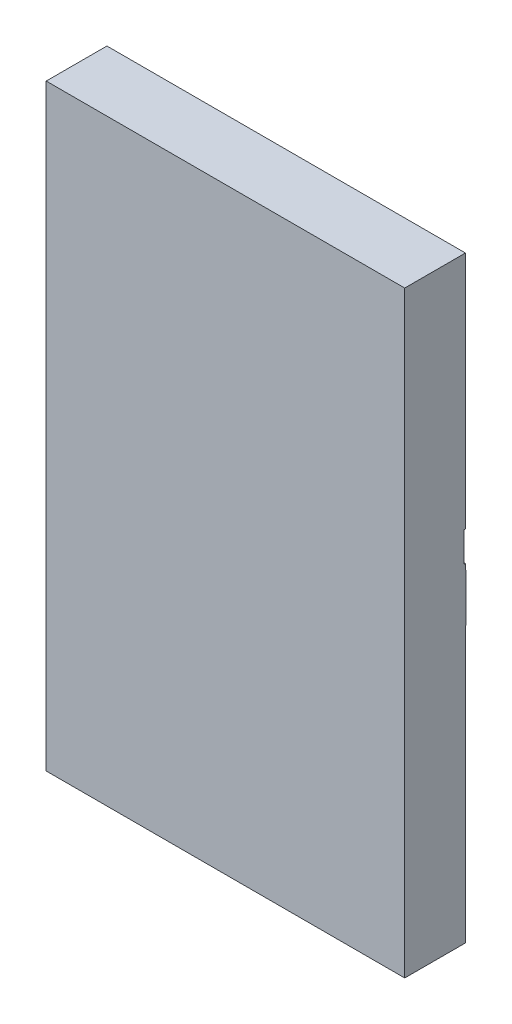
SolidWorks part; units mm, degrees
ref_plane "Front" through (0, 0, 0) normal (0, 0, 1) x (1, 0, 0)
ref_plane "Top" through (0, 0, 0) normal (0, 1, 0) x (1, 0, 0)
ref_plane "Right" through (0, 0, 0) normal (1, 0, 0) x (0, 0, -1)
sketch "Sketch1" plane through (0, 0, 0) normal (0, 0, 1) x (1, 0, 0)
  line L1 (0, 0) -> (3, 0)
  line L2 (0, 0) -> (0, 5)
  line L3 (0, 5) -> (3, 5)
  line L4 (3, 0) -> (3, 5)
  dimension "D1" = 5
  dimension "D2" = 3
extrude "Base-Extrude" add sketch "Sketch1" along normal blind 0.508
sketch "Sketch2" plane through (3, 0, 0) normal (1, 0, 0) x (0, 0, -1)
  line L0 (0, 0) -> (0, 5) construction
  line L1 (0, 3) -> (-0.01, 3)
  line L2 (0, 3) -> (0, 2.75)
  line L3 (0, 2.75) -> (-0.01, 2.75)
  line L4 (-0.01, 3) -> (-0.01, 2.75)
  line L5 (-0.508, 5) -> (0, 5) construction
  dimension "D1" = 2
  dimension "D2" = 0.25
  dimension "D3" = 0.01
extrude "Cut-Extrude1" cut sketch "Sketch2" against normal through all
sketch "Sketch3" plane through (3, 0, 0) normal (1, 0, 0) x (0, 0, -1)
  line L0 (0, 0) -> (0, 2.75) construction
  line L1 (0, 2.7) -> (0.003, 2.7)
  line L2 (0, 2.7) -> (0, 2.3)
  line L3 (0, 2.3) -> (0.003, 2.3)
  line L4 (0.003, 2.7) -> (0.003, 2.3)
  line L5 (-0.508, 0) -> (0, 0) construction
  dimension "D1" = 0.4
  dimension "D2" = 2.3
  dimension "D3" = 0.003
extrude "Boss-Extrude2" add sketch "Sketch3" against normal blind 3
sketch "Sketch4" plane through (0, 0, 0) normal (0, 0, -1) x (-1, 0, 0)
  line L5 (-3, 0) -> (-3, 2.3) construction
  line L7 (0, 2.3) -> (-3, 2.3) construction
  circle A0 centre (-2.9, 2.2) radius 0.02
  dimension "D1" = 0.04
  dimension "Vertical Edge Distance" = 0.1
split line "Split Line10"
sketch "Sketch9" plane through (0, 0, 0) normal (0, 0, -1) x (-1, 0, 0)
  line L0 (-3, 5) -> (0, 5) construction
  line L1 (-2.95, 4.95) -> (-0.05, 4.95)
  line L2 (-2.95, 4.95) -> (-2.95, 3)
  line L3 (0, 3) -> (-3, 3) construction
  line L4 (-0.05, 4.95) -> (-0.05, 3)
  line L5 (-3, 3) -> (-3, 5) construction
  line L6 (0, 5) -> (0, 3) construction
split line "Split Line4"
sketch "Sketch10" plane through (0, 0, 0) normal (0, 0, -1) x (-1, 0, 0)
  line L0 (0, 2.3) -> (-3, 2.3) construction
  line L1 (0, 2.3) -> (0, 0) construction
  circle A0 centre (-0.1, 2.2) radius 0.02
  dimension "D1" = 0.04
  dimension "D2" = 0.1
  dimension "D3" = 0.1
split line "Split Line12"
sketch "Sketch12" plane through (0, 0, 0) normal (0, 0, -1) x (-1, 0, 0)
  line L0 (-0.05, 3) -> (-2.95, 3) construction
  line L1 (0, 5) -> (0, 3) construction
  circle A0 centre (-0.1, 3.1) radius 0.02
  dimension "D1" = 0.04
  dimension "D3" = 0.1
  dimension "D2" = 0.1
split line "Split Line14"
sketch "Sketch13" plane through (0, 0, 0) normal (0, 0, -1) x (-1, 0, 0)
  line L0 (-3, 3) -> (-3, 5) construction
  line L1 (-0.05, 3) -> (-2.95, 3) construction
  circle A0 centre (-2.9, 3.1) radius 0.02
  dimension "D1" = 0.1
  dimension "D2" = 0.1
split line "Split Line15"
sketch "Sketch14" plane through (0, 0, 0) normal (0, 0, -1) x (-1, 0, 0)
  line L0 (-3, 0) -> (-3, 2.3) construction
  line L1 (-0.05, 2.2) -> (0, 2.2)
  line L2 (-2.95, 2.2) -> (-2.95, 0.05)
  line L3 (-2.95, 0.05) -> (-0.05, 0.05)
  line L4 (-0.05, 2.2) -> (-0.05, 0.05)
  line L5 (0, 0) -> (-3, 0) construction
  line L6 (0, 2.3) -> (0, 0) construction
  line L8 (-2.95, 2.2) -> (-3, 2.2)
  line L9 (0, 2.3) -> (-3, 2.3) construction
  dimension "D4" = 0.1
split line "Split Line16"
sketch "Sketch16" plane through (0, 0, -0.003) normal (0, 0, -1) x (-1, 0, 0)
  line L1 (-0.001, 2.25) -> (-2.001, 2.25)
  line L2 (-0.001, 2.25) -> (-0.001, 2.75)
  line L3 (-0.001, 2.75) -> (-2.001, 2.75)
  line L4 (-2.001, 2.25) -> (-2.001, 2.75)
  line L5 (-2.001, 2.5) -> (-0.001, 2.5) construction
  line L6 (0, 2.75) -> (-3, 2.75) construction
  line L7 (0, 2.3) -> (0, 2.7) construction
  dimension "D1" = 0.5
  dimension "D2" = 2
  dimension "D3" = 0.25
  dimension "D4" = 0.001
extrude "Boss-Extrude3" add sketch "Sketch16" along normal blind 0.097
sketch "Sketch17" plane through (0, 0, 0) normal (-1, 0, 0) x (0, 0, 1)
  line L0 (-0.1, 2.25) -> (-0.1, 2.75) construction
  line L1 (-0.1, 2.495) -> (-0.095, 2.495)
  line L2 (-0.1, 2.495) -> (-0.1, 2.505)
  line L3 (-0.1, 2.505) -> (-0.095, 2.505)
  line L4 (-0.095, 2.495) -> (-0.095, 2.505)
  line L5 (-0.1, 2.5) -> (-0.095, 2.5) construction
  line L6 (-0.1, 2.25) -> (-0.003, 2.25) construction
  dimension "D1" = 0.005
  dimension "D2" = 0.01
  dimension "D3" = 0.25
extrude "Cut-Extrude2" cut sketch "Sketch17" against normal through all
